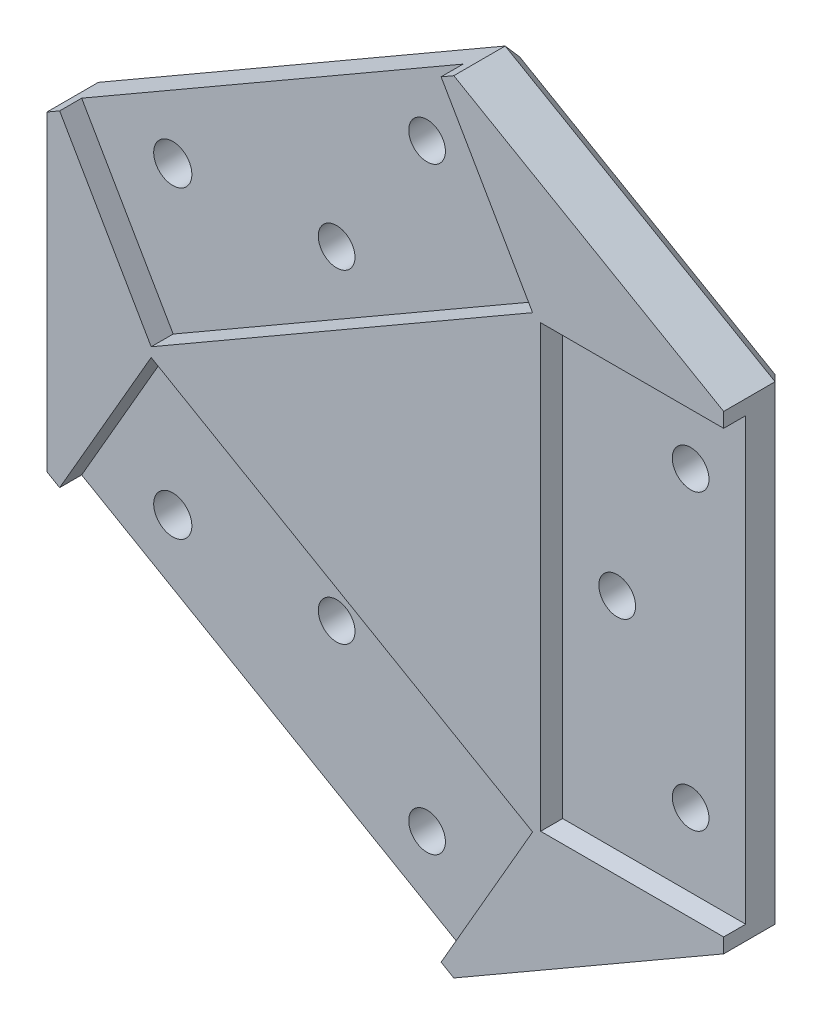
SolidWorks part; units mm, degrees
ref_plane "Front Plane" through (0, 0, 0) normal (0, 0, 1) x (1, 0, 0)
ref_plane "Top Plane" through (0, 0, 0) normal (0, 1, 0) x (1, 0, 0)
ref_plane "Right Plane" through (0, 0, 0) normal (1, 0, 0) x (0, 0, -1)
sketch "Sketch1" plane through (0, 0, 0) normal (0, 0, 1) x (1, 0, 0)
  line L5561 (2912.5938, 936.8509) -> (2902.962, 953.5337)
  line L5562 (2964.5554, 966.8509) -> (2954.9236, 983.5337)
  line L5563 (2961.8842, 958.761) -> (2920.9355, 935.1193)
  line L5564 (2974.1554, 961.3084) -> (2993.4189, 961.3084)
  line L5565 (2974.1554, 901.3084) -> (2993.4189, 901.3084)
  line L5566 (2968.4848, 954.9501) -> (2968.4848, 907.6667)
  line L5567 (2912.5938, 925.7658) -> (2902.962, 909.0831)
  line L5568 (2964.5554, 895.7658) -> (2954.9236, 879.0831)
  line L5569 (2961.8842, 903.8558) -> (2920.9355, 927.4975)
  line L5570 (2993.4189, 963.3084) -> (2993.4189, 899.3084)
  line L5571 (2901.23, 952.5337) -> (2956.6556, 984.5337)
  line L5572 (2901.23, 910.0831) -> (2956.6556, 878.0831)
  line L5573 (2901.23, 910.0831) -> (2901.23, 952.5337)
  line L5574 (2956.6556, 878.0831) -> (2993.4189, 899.3084)
  line L5575 (2956.6556, 984.5337) -> (2993.4189, 963.3084)
  circle A980 centre (2975.9189, 931.3084) radius 2.5
  circle A981 centre (2950.0133, 972.0385) radius 2.5
  circle A982 centre (2915.3723, 952.0385) radius 2.6
  circle A983 centre (2937.6928, 953.3783) radius 2.5
  circle A984 centre (2985.9189, 951.3084) radius 2.5
  circle A985 centre (2985.9189, 911.3084) radius 2.5
  arc A986 (2912.5938, 936.8509) -> (2912.5938, 925.7658) centre (2915.7938, 931.3084) ccw
  arc A987 (2920.9355, 927.4975) -> (2920.9355, 935.1193) centre (2915.7938, 931.3084) ccw
  arc A988 (2964.5554, 895.7658) -> (2974.1554, 901.3084) centre (2967.7554, 901.3084) ccw
  arc A989 (2968.4848, 907.6667) -> (2961.8842, 903.8558) centre (2967.7554, 901.3084) ccw
  arc A990 (2974.1554, 961.3084) -> (2964.5554, 966.8509) centre (2967.7554, 961.3084) ccw
  arc A991 (2961.8842, 958.761) -> (2968.4848, 954.9501) centre (2967.7554, 961.3084) ccw
  circle A992 centre (2950.0133, 890.5783) radius 2.5
  circle A993 centre (2915.3723, 910.5783) radius 2.6
  circle A994 centre (2937.6928, 909.2385) radius 2.5
extrude "Boss-Extrude2" add sketch "Sketch1" along normal blind 9 contours A986 L5561 L5571 L5573 L5572 L5567 | L5564 A990 L5562 L5571 L5561 A986 L5567 L5572 L5568 A988 L5565 L5570 A994 A993 A992 A985 A984 A983 A982 A981 A980 L5563 A991 L5566 A989 L5569 A987 | A990 L5564 L5570 L5575 L5571 L5562 | A991 L5563 A987 L5569 A989 L5566 | A988 L5568 L5572 L5574 L5570 L5565
sketch "Sketch3" plane through (0, 0, 9) normal (0, 0, 1) x (1, 0, 0)
  line L0 (2993.4189, 963.3084) -> (2993.4189, 899.3084) construction
  line L1 (2956.6556, 878.0831) -> (2993.4189, 899.3084) construction
  line L2 (2901.23, 910.0831) -> (2956.6556, 878.0831) construction
  line L3 (2901.23, 910.0831) -> (2901.23, 952.5337) construction
  line L4 (2901.23, 952.5337) -> (2956.6556, 984.5337) construction
  line L5 (2956.6556, 984.5337) -> (2993.4189, 963.3084) construction
  line L6 (2961.8842, 958.761) -> (2920.9355, 935.1193) construction
  line L7 (2968.4848, 954.9501) -> (2968.4848, 907.6667) construction
  line L8 (2961.8842, 903.8558) -> (2920.9355, 927.4975) construction
  line L9 (2974.1554, 901.3084) -> (2993.4189, 901.3084) construction
  line L10 (2964.5554, 895.7658) -> (2954.9236, 879.0831) construction
  line L11 (2912.5938, 925.7658) -> (2902.962, 909.0831) construction
  line L12 (2912.5938, 936.8509) -> (2902.962, 953.5337) construction
  line L13 (2964.5554, 966.8509) -> (2954.9236, 983.5337) construction
  line L14 (2974.1554, 961.3084) -> (2993.4189, 961.3084) construction
  line L15 (2993.4189, 963.3084) -> (2993.4189, 899.3084)
  line L16 (2956.6556, 878.0831) -> (2993.4189, 899.3084)
  line L17 (2901.23, 910.0831) -> (2956.6556, 878.0831)
  line L18 (2901.23, 910.0831) -> (2901.23, 952.5337)
  line L19 (2901.23, 952.5337) -> (2956.6556, 984.5337)
  line L20 (2956.6556, 984.5337) -> (2993.4189, 963.3084)
  line L21 (2967.3906, 961.9401) -> (2915.4291, 931.9401)
  line L22 (2968.4848, 961.3084) -> (2968.4848, 901.3084)
  line L23 (2967.3906, 900.6766) -> (2915.4291, 930.6766)
  line L24 (2968.4848, 901.3084) -> (2993.4189, 901.3084)
  line L25 (2967.3906, 900.6766) -> (2954.9236, 879.0831)
  line L26 (2915.4291, 930.6766) -> (2902.962, 909.0831)
  line L27 (2915.4291, 931.9401) -> (2902.962, 953.5337)
  line L28 (2967.3906, 961.9401) -> (2954.9236, 983.5337)
  line L29 (2968.4848, 961.3084) -> (2993.4189, 961.3084)
  circle A0 centre (2937.6928, 953.3783) radius 2.5 construction
  circle A1 centre (2915.3723, 952.0385) radius 2.6 construction
  circle A2 centre (2950.0133, 972.0385) radius 2.5 construction
  circle A3 centre (2975.9189, 931.3084) radius 2.5 construction
  circle A7 centre (2937.6928, 909.2385) radius 2.5 construction
  circle A8 centre (2915.3723, 910.5783) radius 2.6 construction
  circle A9 centre (2950.0133, 890.5783) radius 2.5 construction
  circle A10 centre (2985.9189, 911.3084) radius 2.5 construction
  circle A11 centre (2985.9189, 951.3084) radius 2.5 construction
  circle A15 centre (2937.6928, 953.3783) radius 2.5
  circle A16 centre (2915.3723, 952.0385) radius 2.6
  circle A17 centre (2950.0133, 972.0385) radius 2.5
  circle A18 centre (2975.9189, 931.3084) radius 2.5
  circle A22 centre (2937.6928, 909.2385) radius 2.5
  circle A23 centre (2915.3723, 910.5783) radius 2.6
  circle A24 centre (2950.0133, 890.5783) radius 2.5
  circle A25 centre (2985.9189, 911.3084) radius 2.5
  circle A26 centre (2985.9189, 951.3084) radius 2.5
  circle M7 centre (2937.6928, 909.2385) radius 2.5
  circle M8 centre (2915.3723, 910.5783) radius 2.6
  circle M9 centre (2950.0133, 890.5783) radius 2.5
  circle M10 centre (2985.9189, 911.3084) radius 2.5
  circle M11 centre (2985.9189, 951.3084) radius 2.5
  circle M12 centre (2937.6928, 953.3783) radius 2.5
  circle M13 centre (2915.3723, 952.0385) radius 2.6
  circle M14 centre (2950.0133, 972.0385) radius 2.5
  circle M15 centre (2975.9189, 931.3084) radius 2.5
chamfer "Chamfer1" distance 2 angle 45 6 edges at (2975.0373, 973.921, 0) (2928.9428, 968.5337, 0) (2901.23, 931.3084, 0) (2928.9428, 894.0831, 0) (2975.0373, 888.6957, 0) (2993.4189, 931.3084, 0)
extrude "Cut-Extrude1" cut sketch "Sketch3" against normal blind 3 contours L23 L26 L17 L25 M8 M9 M7 | L21 L28 L19 L27 M12 M14 M13 | L29 L22 L24 L15 M11 M15 M10
